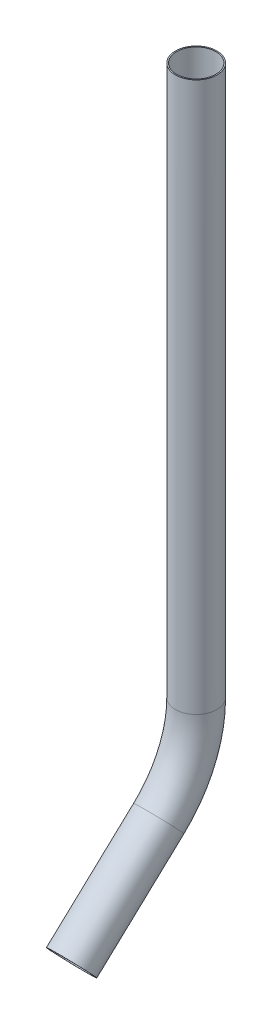
SolidWorks part; units mm, degrees
ref_plane "Front Plane" through (0, 0, 0) normal (0, 0, 1) x (1, 0, 0)
ref_plane "Top Plane" through (0, 0, 0) normal (0, 1, 0) x (1, 0, 0)
ref_plane "Right Plane" through (0, 0, 0) normal (1, 0, 0) x (0, 0, -1)
sketch "Sketch1" plane through (0, 0, 0) normal (0, 1, 0) x (1, 0, 0)
  circle A0 centre (0, 0) radius 6.731
  circle A1 centre (0, 0) radius 6.35
  dimension "D1" = 13.462
  dimension "D2" = 12.7
sketch "Sketch2" plane through (0, 0, 0) normal (1, 0, 0) x (0, 0, -1)
  line L0 (0, 0) -> (0, -177.8)
  line L1 (-12.1129, -205.6618) -> (-40.3156, -231.967)
  arc A0 (0, -177.8) -> (-12.1129, -205.6618) centre (-38.1, -177.8) cw
  point P5 (-10.5894, -216.3277)
  dimension "D1" = 38.1
  dimension "D2" = 177.8
sweep "Sweep1" add profiles "Sketch1" path "Sketch2"
